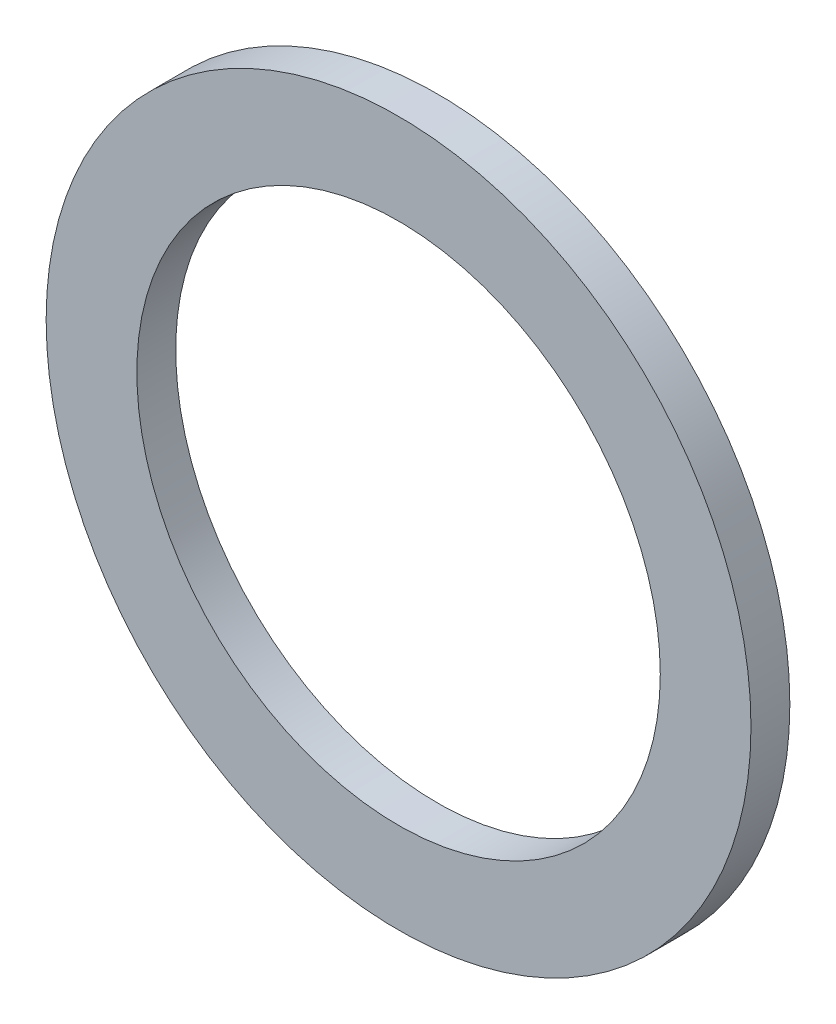
SolidWorks part; units mm, degrees
ref_plane "Front Plane" through (0, 0, 0) normal (0, 0, 1) x (1, 0, 0)
ref_plane "Top Plane" through (0, 0, 0) normal (0, 1, 0) x (1, 0, 0)
ref_plane "Right Plane" through (0, 0, 0) normal (1, 0, 0) x (0, 0, -1)
sketch "Sketch1" plane through (0, 0, 0) normal (0, 0, 1) x (1, 0, 0)
  circle A0 centre (0, 0) radius 13.6
  dimension "D1" = 27.2
extrude "Boss-Extrude1" add sketch "Sketch1" along normal blind 1.5
sketch "Sketch2" plane through (0, 0, 1.5) normal (0, 0, 1) x (1, 0, 0)
  circle A0 centre (0, 0) radius 10.1
  dimension "D1" = 20.2
extrude "Cut-Extrude1" cut sketch "Sketch2" against normal blind 1.5
